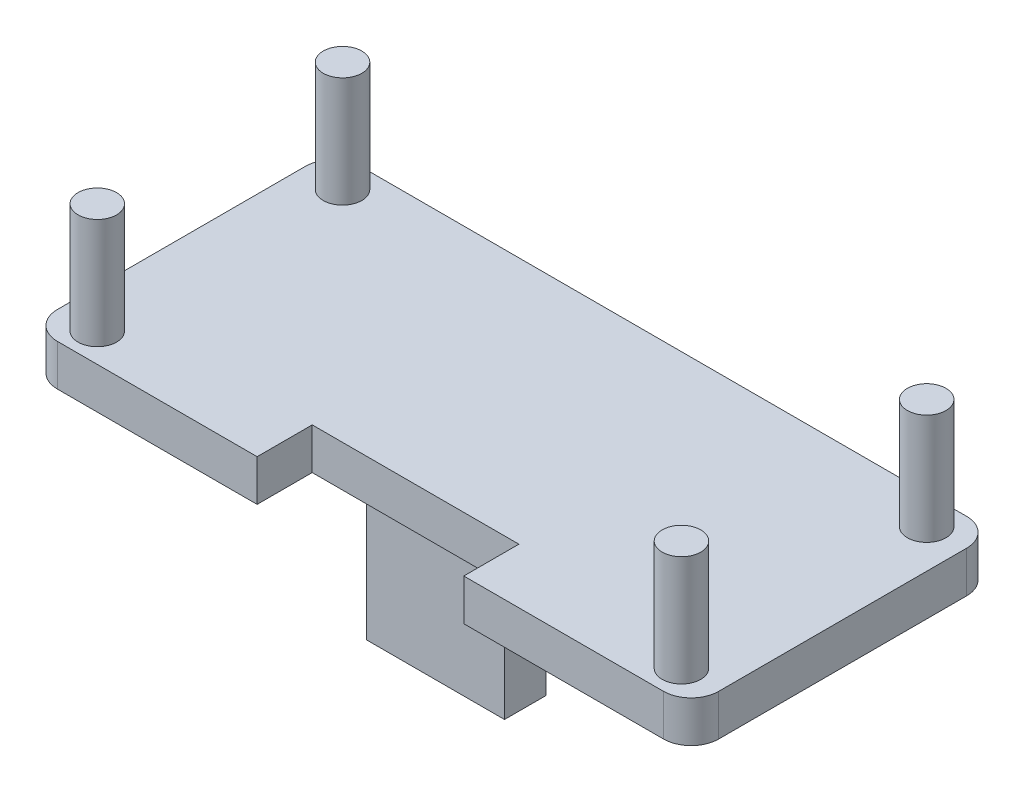
SolidWorks part; units mm, degrees
ref_plane "Front Plane" through (0, 0, 0) normal (0, 0, 1) x (1, 0, 0)
ref_plane "Top Plane" through (0, 0, 0) normal (0, 1, 0) x (1, 0, 0)
ref_plane "Right Plane" through (0, 0, 0) normal (1, 0, 0) x (0, 0, -1)
sketch "Sketch1" plane through (0, 0, 0) normal (0, 1, 0) x (1, 0, 0)
  line L1 (-24, -11) -> (24, -11)
  line L2 (-24, -11) -> (-24, 11)
  line L3 (-24, 11) -> (24, 11)
  line L4 (24, -11) -> (24, 11)
  line L5 (-24, -11) -> (24, 11) construction
  line L6 (-24, 11) -> (24, -11) construction
  point P0 (0, 0)
  dimension "D1" = 48
  dimension "D2" = 22
extrude "Boss-Extrude1" add sketch "Sketch1" along normal blind 3
sketch "Sketch2" plane through (0, 3, 0) normal (0, 1, 0) x (1, 0, 0)
  line L1 (-22.6, -10.3) -> (22.6, -10.3)
  line L2 (-22.6, -10.3) -> (-22.6, 10.3)
  line L3 (-22.6, 10.3) -> (22.6, 10.3)
  line L4 (22.6, -10.3) -> (22.6, 10.3)
  line L5 (-22.6, -10.3) -> (22.6, 10.3) construction
  line L6 (-22.6, 10.3) -> (22.6, -10.3) construction
  circle A0 centre (-21.2, -8.9) radius 1.4
  circle A1 centre (-21.2, 8.9) radius 1.4
  circle A2 centre (21.2, -8.9) radius 1.4
  circle A3 centre (21.2, 8.9) radius 1.4
  point P0 (0, 0)
  dimension "D3" = 2.8
  dimension "D1" = 45.2
  dimension "D2" = 20.6
extrude "Boss-Extrude2" add sketch "Sketch2" along normal blind 8 contours A1 | A0 | A3 | A2
sketch "Sketch3" plane through (0, 0, 0) normal (0, -1, 0) x (1, 0, 0)
  line L8 (-5, 2.5448) -> (5, 2.5448)
  line L9 (-5, 2.5448) -> (-5, 5.5448)
  line L10 (-5, 5.5448) -> (5, 5.5448)
  line L11 (5, 2.5448) -> (5, 5.5448)
  line L12 (-5, 2.5448) -> (5, 5.5448) construction
  line L13 (-5, 5.5448) -> (5, 2.5448) construction
  point P14 (0, 4.0448)
  dimension "D3" = 3
  dimension "D4" = 10
extrude "Boss-Extrude3" add sketch "Sketch3" along normal blind 10
sketch "Sketch4" plane through (0, 0, 0) normal (0, -1, 0) x (1, 0, 0)
  line L1 (-24, 11) -> (24, 11) construction
  line L3 (-7.5, 7) -> (7.5, 7)
  line L4 (-7.5, 7) -> (-7.5, 11)
  line L5 (-7.5, 11) -> (7.5, 11)
  line L6 (7.5, 7) -> (7.5, 11)
  line L7 (-7.5, 7) -> (7.5, 11) construction
  line L8 (-7.5, 11) -> (7.5, 7) construction
  point P5 (0, 9)
  dimension "D1" = 15
  dimension "D2" = 4
extrude "Cut-Extrude1" cut sketch "Sketch4" against normal blind 10
fillet "Fillet1" radius 2 4 edges at (24, 1.5, 11) (-24, 1.5, 11) (-24, 1.5, -11) (24, 1.5, -11)
